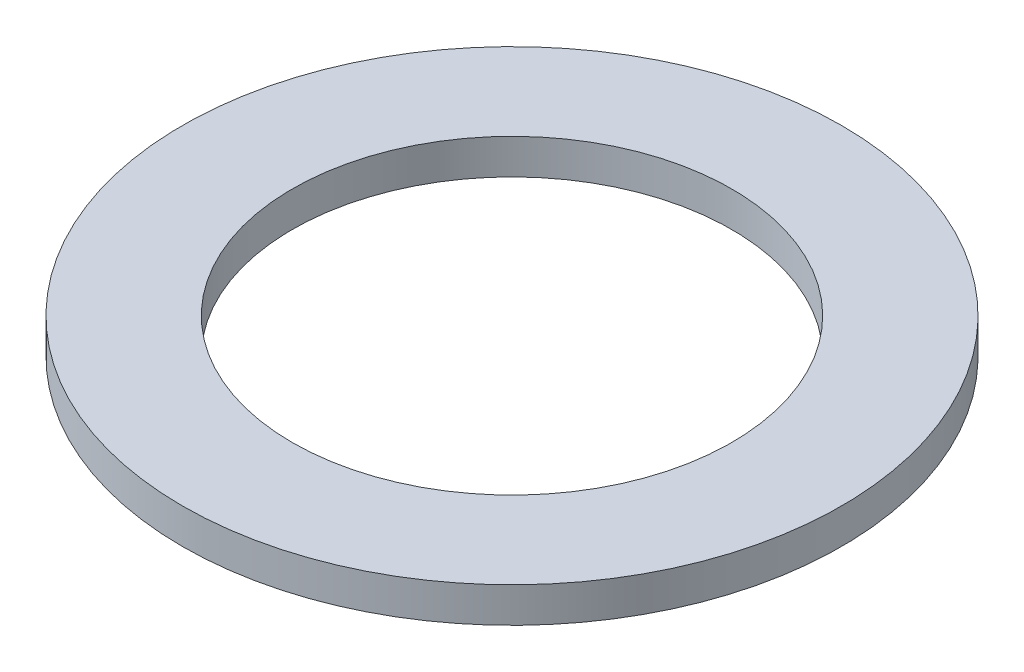
SolidWorks part; units mm, degrees
ref_plane "Front Plane" through (0, 0, 0) normal (0, 0, 1) x (1, 0, 0)
ref_plane "Top Plane" through (0, 0, 0) normal (0, 1, 0) x (1, 0, 0)
ref_plane "Right Plane" through (0, 0, 0) normal (1, 0, 0) x (0, 0, -1)
sketch "Sketch1" plane through (0, 0, 0) normal (0, 1, 0) x (1, 0, 0)
  circle A0 centre (0, 0) radius 9.525
  circle A1 centre (0, 0) radius 6.35
  dimension "D1" = 19.05
  dimension "D2" = 12.7
extrude "Boss-Extrude1" add sketch "Sketch1" along normal blind 1.016
